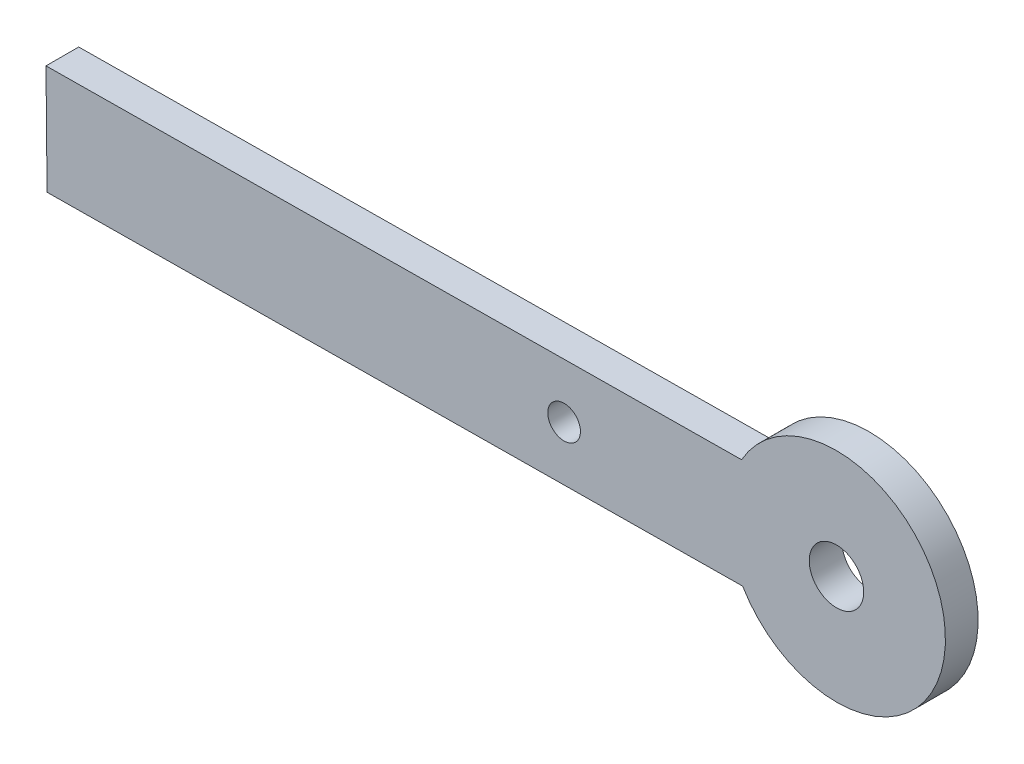
SolidWorks part; units mm, degrees
ref_plane "Front Plane" through (0, 0, 0) normal (0, 0, 1) x (1, 0, 0)
ref_plane "Top Plane" through (0, 0, 0) normal (0, 1, 0) x (1, 0, 0)
ref_plane "Right Plane" through (0, 0, 0) normal (1, 0, 0) x (0, 0, -1)
sketch "Sketch1" plane through (0, 0, 0) normal (0, 0, 1) x (1, 0, 0)
  line L2 (21.5824, 58.3169) -> (102.7094, 0.3774) construction
  line L4 (9.4075, -80.4493) -> (128.4969, -165.5009) construction
  line L8 (83.6973, 13.9554) -> (13.9554, -83.6973) construction
  line L10 (-36.7445, 67.3435) -> (27.0955, 67.9588)
  line L11 (-36.7445, 67.3435) -> (-36.6481, 57.344)
  line L12 (-36.6481, 57.344) -> (27.1919, 57.9593)
  line L13 (35.8036, 63.0425) -> (-70.465, 62.0183) construction
  line L14 (87.7662, 11.0495) -> (18.0243, -86.6033) construction
  circle A9 centre (0, 0) radius 60 construction
  circle A11 centre (35.8036, 63.0425) radius 2.5
  circle A12 centre (10.8047, 62.8016) radius 1.5
  circle A14 centre (35.8036, 63.0425) radius 72.5032 construction
  arc A16 (27.1919, 57.9593) -> (27.0955, 67.9588) centre (35.8036, 63.0425) ccw
  circle A17 centre (97.9149, -69.9291) radius 60 construction
  point P14 (0, 0)
  point P17 (-1.7695, 72.5)
  point P22 (0, 0)
  point P25 (0, 0)
  point P26 (-1.7695, 72.5)
  point P28 (0, 0)
  point P29 (49.2631, 20.9727)
  point P30 (-22.7856, 63.5758)
  point P31 (0, 0)
  point P33 (-23.0107, 72.5)
  point P34 (-40.6796, 72.5)
  point P35 (-67.224, 27.151)
  point P36 (-118.3172, 73.4058)
  point P37 (35.8036, 62.8016)
  dimension "D2" = 120
  dimension "D3" = 120
  dimension "D4" = 5
  dimension "D5" = 5
  dimension "D6" = 5
  dimension "D10" = 72.5
  dimension "D8" = 25
  dimension "D9" = 3
  dimension "D11" = 120
  dimension "D12" = 5
  dimension "D7" = 10
  dimension "D13" = 63.84
extrude "Boss-Extrude1" add sketch "Sketch1" along normal blind 3
